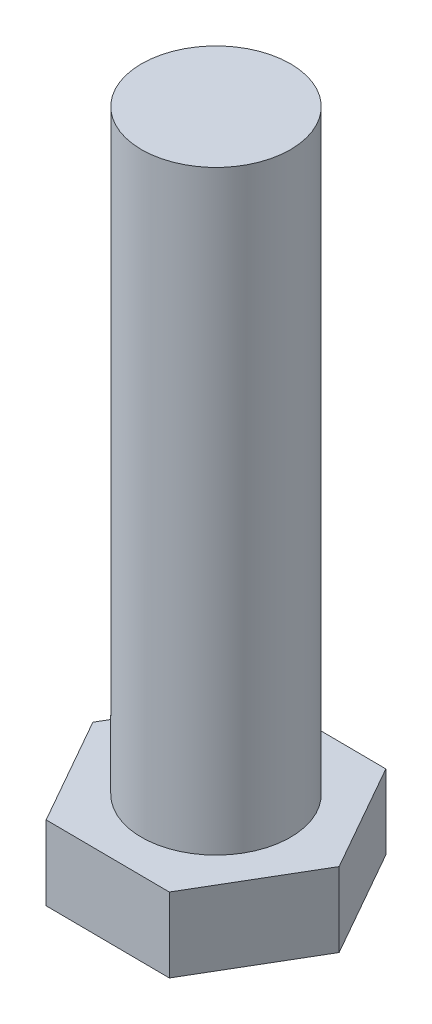
SolidWorks part; units mm, degrees
ref_plane "Front Plane" through (0, 0, 0) normal (0, 0, 1) x (1, 0, 0)
ref_plane "Top Plane" through (0, 0, 0) normal (0, 1, 0) x (1, 0, 0)
ref_plane "Right Plane" through (0, 0, 0) normal (1, 0, 0) x (0, 0, -1)
sketch "Sketch1" plane through (0, 0, 0) normal (0, 1, 0) x (1, 0, 0)
  circle A0 centre (0, 0) radius 1.5
  dimension "D1" = 3
extrude "Boss-Extrude1" add sketch "Sketch1" along normal blind 12
sketch "Sketch2" plane through (0, 0, 0) normal (0, -1, 0) x (1, 0, 0)
  line L1 (2.5, 0.0189) -> (1.2336, 2.1745)
  line L2 (1.2336, 2.1745) -> (-1.2664, 2.1556)
  line L3 (-1.2664, 2.1556) -> (-2.5, -0.0189)
  line L4 (-2.5, -0.0189) -> (-1.2336, -2.1745)
  line L5 (-1.2336, -2.1745) -> (1.2664, -2.1556)
  line L6 (1.2664, -2.1556) -> (2.5, 0.0189)
  circle A0 centre (0, 0) radius 2.1651 construction
  dimension "D1" = 2.5
extrude "Boss-Extrude2" add sketch "Sketch2" along normal blind 1.5
equation "\"thread_dist\"= 3.5"
equation "\"thread_diameter\"= 3"
equation "\"D13@Sketch1\"=\"thread_diameter\""
equation "\"D14@Sketch1\"=\"thread_dist\""
equation "\"D11@Sketch1\"=\"thread_diameter\""
equation "\"D12@Sketch1\"=\"thread_dist\""
equation "\"D8@Sketch1\"=\"thread_diameter\""
equation "\"D10@Sketch1\"=\"thread_dist\""
equation "\"D1@Sketch1\"=\"thread_diameter\""
equation "\"thread_length\"=12"
equation "\"D1@Boss-Extrude1\"=\"thread_length\""
